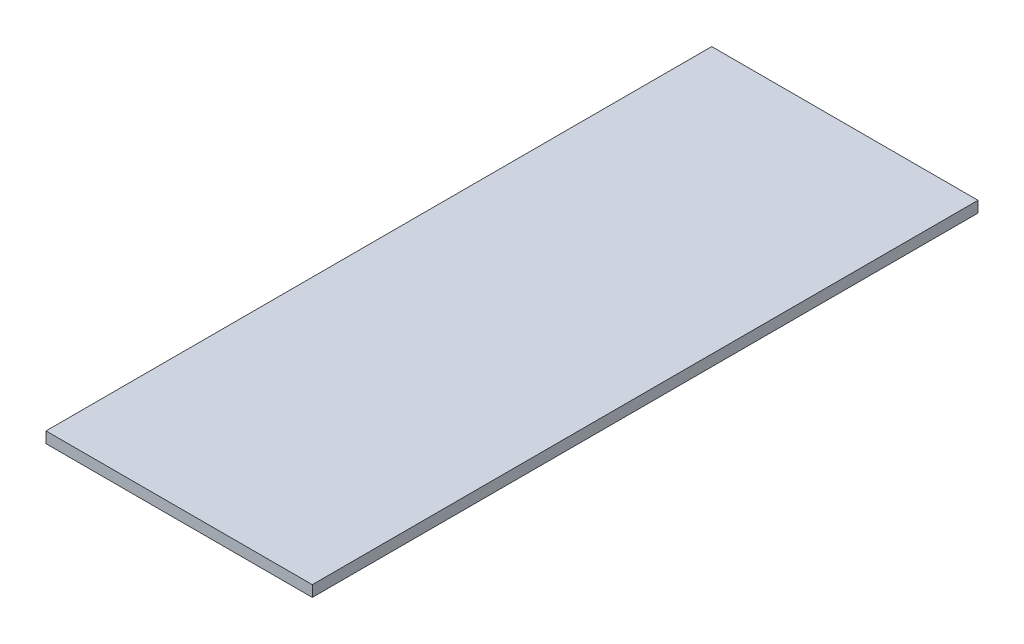
SolidWorks part; units mm, degrees
ref_plane "Front Plane" through (0, 0, 0) normal (0, 0, 1) x (1, 0, 0)
ref_plane "Top Plane" through (0, 0, 0) normal (0, 1, 0) x (1, 0, 0)
ref_plane "Right Plane" through (0, 0, 0) normal (1, 0, 0) x (0, 0, -1)
sketch "Sketch1" plane through (0, 0, 0) normal (0, 1, 0) x (1, 0, 0)
  line L1 (0, 0) -> (152.4, 0)
  line L2 (0, 0) -> (0, 381)
  line L3 (0, 381) -> (152.4, 381)
  line L4 (152.4, 0) -> (152.4, 381)
  dimension "D1" = 381
  dimension "D2" = 152.4
extrude "Boss-Extrude1" add sketch "Sketch1" along normal blind 6.35
